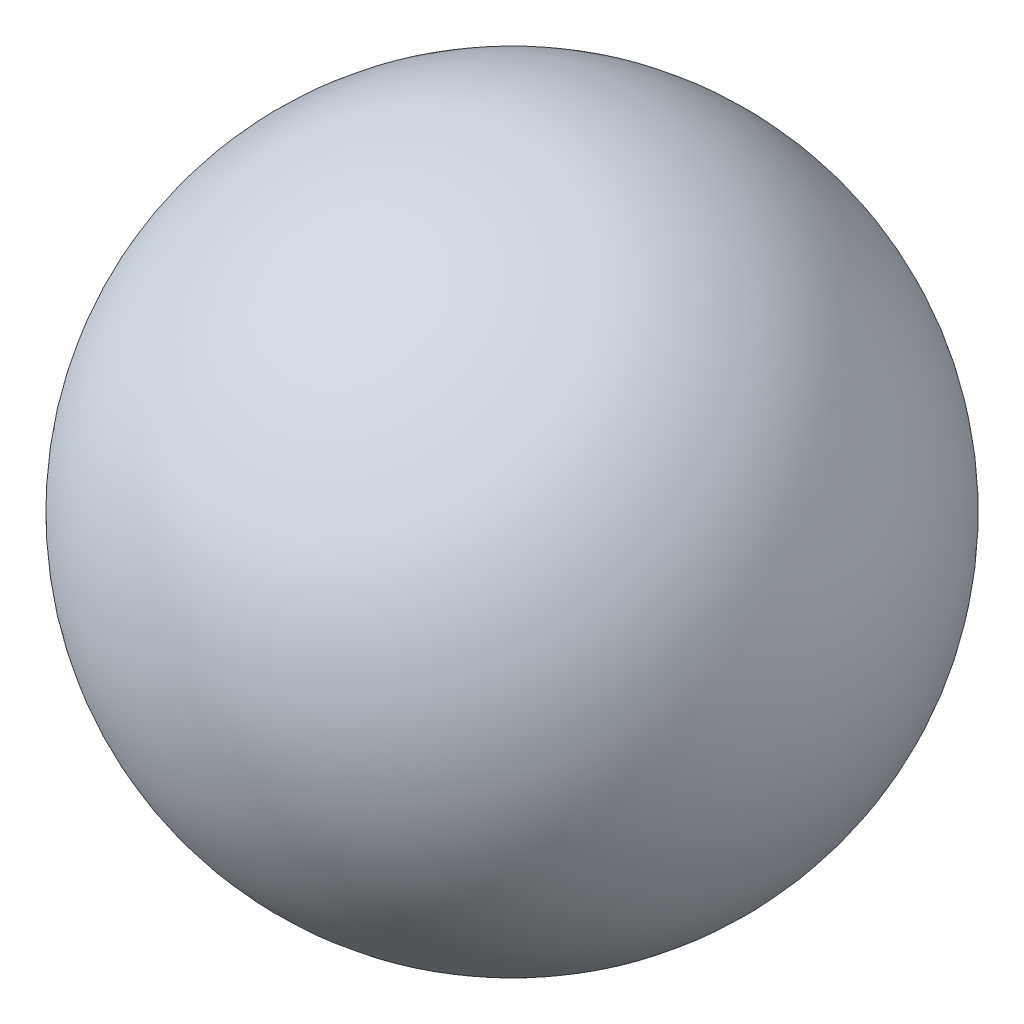
SolidWorks part; units mm, degrees
ref_plane "Alzado" through (0, 0, 0) normal (0, 0, 1) x (1, 0, 0)
ref_plane "Planta" through (0, 0, 0) normal (0, 1, 0) x (1, 0, 0)
ref_plane "Vista lateral" through (0, 0, 0) normal (1, 0, 0) x (0, 0, -1)
sketch "Croquis1" plane through (0, 0, 0) normal (0, 0, 1) x (1, 0, 0)
  line L3 (0, 110) -> (0, -110)
  arc A0 (0, -110) -> (0, 110) centre (0, 0) ccw
  dimension "D1" = 220
revolve "Revolución2" add sketch "Croquis1" angle 360 about L3
